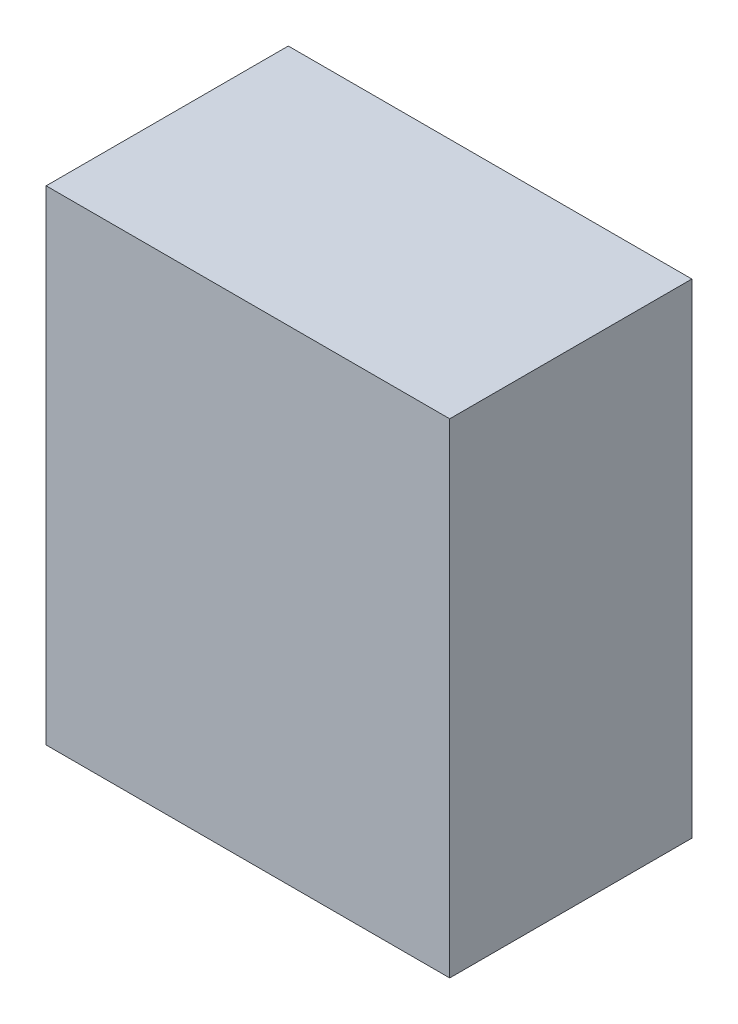
SolidWorks part; units mm, degrees
ref_plane "Front Plane" through (0, 0, 0) normal (0, 0, 1) x (1, 0, 0)
ref_plane "Top Plane" through (0, 0, 0) normal (0, 1, 0) x (1, 0, 0)
ref_plane "Right Plane" through (0, 0, 0) normal (1, 0, 0) x (0, 0, -1)
sketch "Sketch1" plane through (0, 0, 0) normal (0, 0, 1) x (1, 0, 0)
  line L1 (-125, -150) -> (125, -150)
  line L2 (-125, -150) -> (-125, 150)
  line L3 (-125, 150) -> (125, 150)
  line L4 (125, -150) -> (125, 150)
  line L5 (-125, -150) -> (125, 150) construction
  line L6 (-125, 150) -> (125, -150) construction
  point P0 (0, 0)
  dimension "D1" = 250
  dimension "D2" = 300
extrude "Boss-Extrude1" add sketch "Sketch1" along normal blind 150
